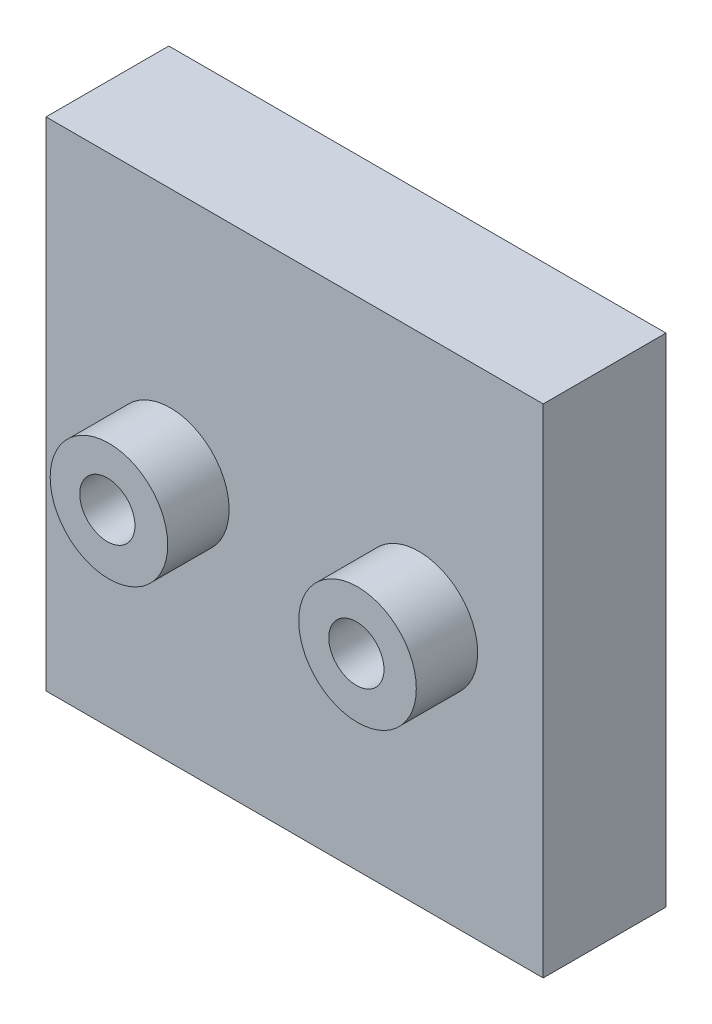
SolidWorks part; units mm, degrees
ref_plane "Front Plane" through (0, 0, 0) normal (0, 0, 1) x (1, 0, 0)
ref_plane "Top Plane" through (0, 0, 0) normal (0, 1, 0) x (1, 0, 0)
ref_plane "Right Plane" through (0, 0, 0) normal (1, 0, 0) x (0, 0, -1)
sketch "Sketch1" plane through (0, 0, 0) normal (0, 1, 0) x (1, 0, 0)
  line L0 (0, 0) -> (0, 78.8911) construction
  line L2 (-40.5, 10) -> (40.5, 10)
  line L3 (-40.5, 10) -> (-40.5, -10)
  line L4 (-40.5, -10) -> (40.5, -10)
  line L5 (40.5, 10) -> (40.5, -10)
  line L6 (-40.5, 10) -> (40.5, -10) construction
  line L7 (-40.5, -10) -> (40.5, 10) construction
  dimension "D1" = 81
  dimension "D2" = 20
extrude "Boss-Extrude2" add sketch "Sketch1" along normal blind 81 contours L2 L5 L4 L3
sketch "Sketch2" plane through (0, 0, 10) normal (0, 0, 1) x (1, 0, 0)
  circle A0 centre (-20.25, 40.5) radius 9.5758
  circle A1 centre (20.25, 40.5) radius 9.5758
extrude "Boss-Extrude4" add sketch "Sketch2" along normal blind 10
sketch "Sketch4" plane through (0, 0, 20) normal (0, 0, 1) x (1, 0, 0)
  circle A0 centre (-20.5109, 40.5563) radius 4.4958
  circle A1 centre (20.0601, 40.5563) radius 4.4958
extrude "Cut-Extrude1" cut sketch "Sketch4" against normal blind 10
